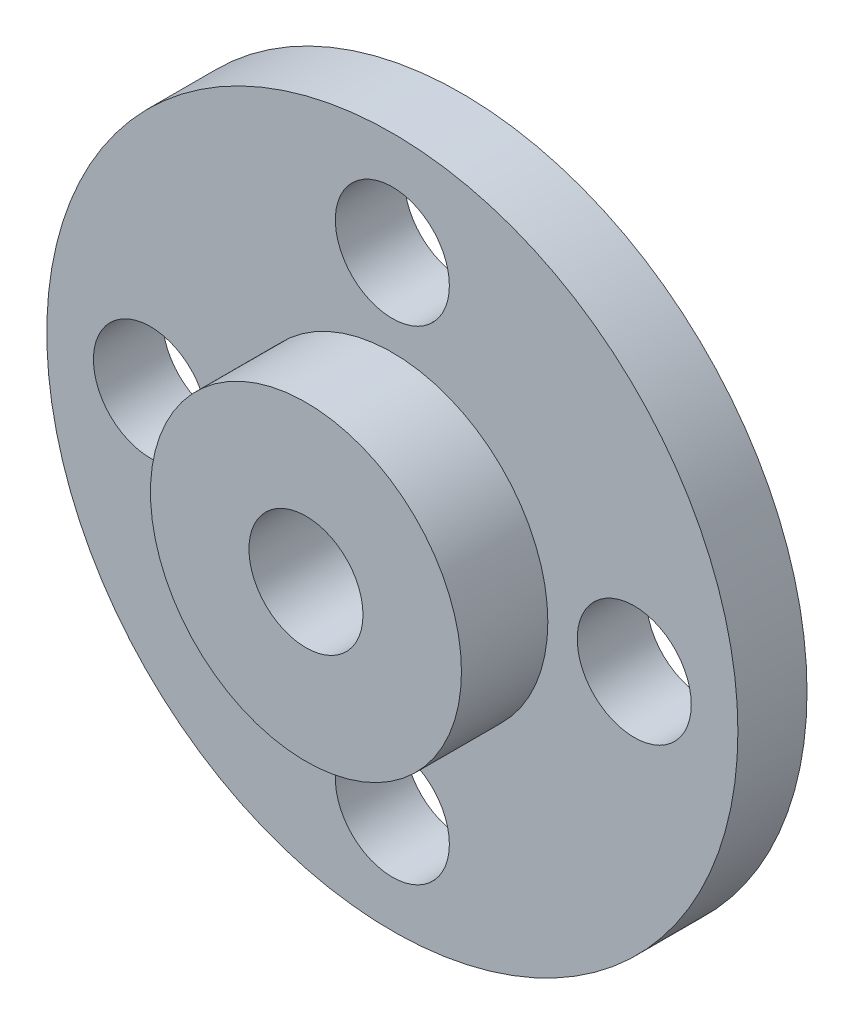
SolidWorks part; units mm, degrees
ref_plane "前视基准面" through (0, 0, 0) normal (0, 0, 1) x (1, 0, 0)
ref_plane "上视基准面" through (0, 0, 0) normal (0, 1, 0) x (1, 0, 0)
ref_plane "右视基准面" through (0, 0, 0) normal (1, 0, 0) x (0, 0, -1)
sketch "草图1" plane through (0, 0, 0) normal (0, 0, 1) x (1, 0, 0)
  circle A0 centre (0, 0) radius 10
  dimension "D1" = 20
extrude "凸台-拉伸1" add sketch "草图1" along normal blind 2
sketch "草图2" plane through (0, 0, 2) normal (0, 0, 1) x (1, 0, 0)
  circle A0 centre (0, 0) radius 4.5
  dimension "D1" = 9
extrude "凸台-拉伸2" add sketch "草图2" along normal blind 2.5
sketch "草图3" plane through (0, 0, 4.5) normal (0, 0, 1) x (1, 0, 0)
  circle A0 centre (0, 0) radius 1.65
  dimension "D1" = 3.3
extrude "切除-拉伸1" cut sketch "草图3" against normal blind 8.5
sketch "草图4" plane through (0, 0, 2) normal (0, 0, 1) x (1, 0, 0)
  circle A0 centre (0, 0) radius 7 construction
  circle A1 centre (0, 7) radius 1.65
  circle A2 centre (7, 0) radius 1.65
  circle A3 centre (0, -7) radius 1.65
  circle A4 centre (-7, 0) radius 1.65
  point P14 (0, 0)
  dimension "D1" = 14
  dimension "D2" = 3.3
  dimension "D3" = 4
extrude "切除-拉伸2" cut sketch "草图4" against normal blind 8.5
